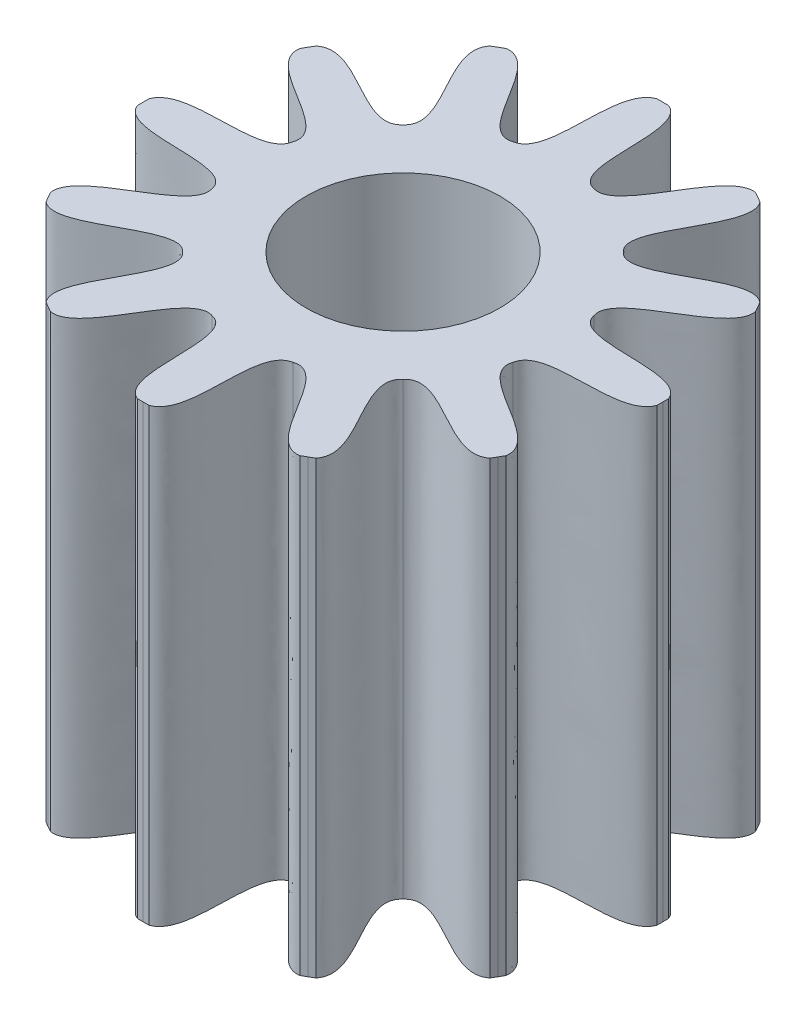
SolidWorks part; units mm, degrees
ref_plane "Alzado" through (0, 0, 0) normal (0, 0, 1) x (1, 0, 0)
ref_plane "Planta" through (0, 0, 0) normal (0, 1, 0) x (1, 0, 0)
ref_plane "Vista lateral" through (0, 0, 0) normal (1, 0, 0) x (0, 0, -1)
sketch "Sketch1" plane through (0, 0, 0) normal (0, 1, 0) x (1, 0, 0)
  line L0 (0, -1000) -> (0, 49000) construction
  line L1 (0, 0) -> (12940.9523, 48296.2913) construction
  line L2 (0, 0.75) -> (0.017, 0.7498)
  line L3 (0, 0.75) -> (-0.017, 0.7498)
  line L4 (0.375, 0.6495) -> (0.3602, 0.6579)
  line L5 (0.375, 0.6495) -> (0.3896, 0.6409)
  line L6 (0.6495, 0.375) -> (0.6409, 0.3896)
  line L7 (0.6495, 0.375) -> (0.6579, 0.3602)
  line L8 (0.75, 0) -> (0.7498, 0.017)
  line L9 (0.75, 0) -> (0.7498, -0.017)
  line L10 (0.6495, -0.375) -> (0.6579, -0.3602)
  line L11 (0.6495, -0.375) -> (0.6409, -0.3896)
  line L12 (0.375, -0.6495) -> (0.3896, -0.6409)
  line L13 (0.375, -0.6495) -> (0.3602, -0.6579)
  line L14 (0, -0.75) -> (0.017, -0.7498)
  line L15 (0, -0.75) -> (-0.017, -0.7498)
  line L16 (-0.375, -0.6495) -> (-0.3602, -0.6579)
  line L17 (-0.375, -0.6495) -> (-0.3896, -0.6409)
  line L18 (-0.6495, -0.375) -> (-0.6409, -0.3896)
  line L19 (-0.6495, -0.375) -> (-0.6579, -0.3602)
  line L20 (-0.75, 0) -> (-0.7498, -0.017)
  line L21 (-0.75, 0) -> (-0.7498, 0.017)
  line L22 (-0.6495, 0.375) -> (-0.6579, 0.3602)
  line L23 (-0.6495, 0.375) -> (-0.6409, 0.3896)
  line L24 (-0.375, 0.6495) -> (-0.3896, 0.6409)
  line L25 (-0.375, 0.6495) -> (-0.3602, 0.6579)
  circle A0 centre (0, 0) radius 0.75 construction
  circle A1 centre (0, 0) radius 0.45 construction
  spline S0 degree 3 poles (0.017, 0.7498) (0.1074, 0.7157) (0.0247, 0.4521) (0.1165, 0.4347) knots 0 0 0 0 1 1 1 1
  spline S1 degree 3 poles (-0.017, 0.7498) (-0.1074, 0.7157) (-0.0247, 0.4521) (-0.1165, 0.4347) knots 0 0 0 0 1 1 1 1
  spline S2 degree 3 poles (0.3602, 0.6579) (0.2649, 0.6735) (0.2047, 0.4039) (0.1165, 0.4347) knots 0 0 0 0 1 1 1 1
  spline S3 degree 3 poles (0.3896, 0.6409) (0.4509, 0.5661) (0.2474, 0.3792) (0.3182, 0.3182) knots 0 0 0 0 1 1 1 1
  spline S4 degree 3 poles (0.6409, 0.3896) (0.5661, 0.4509) (0.3792, 0.2474) (0.3182, 0.3182) knots 0 0 0 0 1 1 1 1
  spline S5 degree 3 poles (0.6579, 0.3602) (0.6735, 0.2649) (0.4039, 0.2047) (0.4347, 0.1165) knots 0 0 0 0 1 1 1 1
  spline S6 degree 3 poles (0.7498, 0.017) (0.7157, 0.1074) (0.4521, 0.0247) (0.4347, 0.1165) knots 0 0 0 0 1 1 1 1
  spline S7 degree 3 poles (0.7498, -0.017) (0.7157, -0.1074) (0.4521, -0.0247) (0.4347, -0.1165) knots 0 0 0 0 1 1 1 1
  spline S8 degree 3 poles (0.6579, -0.3602) (0.6735, -0.2649) (0.4039, -0.2047) (0.4347, -0.1165) knots 0 0 0 0 1 1 1 1
  spline S9 degree 3 poles (0.6409, -0.3896) (0.5661, -0.4509) (0.3792, -0.2474) (0.3182, -0.3182) knots 0 0 0 0 1 1 1 1
  spline S10 degree 3 poles (0.3896, -0.6409) (0.4509, -0.5661) (0.2474, -0.3792) (0.3182, -0.3182) knots 0 0 0 0 1 1 1 1
  spline S11 degree 3 poles (0.3602, -0.6579) (0.2649, -0.6735) (0.2047, -0.4039) (0.1165, -0.4347) knots 0 0 0 0 1 1 1 1
  spline S12 degree 3 poles (0.017, -0.7498) (0.1074, -0.7157) (0.0247, -0.4521) (0.1165, -0.4347) knots 0 0 0 0 1 1 1 1
  spline S13 degree 3 poles (-0.017, -0.7498) (-0.1074, -0.7157) (-0.0247, -0.4521) (-0.1165, -0.4347) knots 0 0 0 0 1 1 1 1
  spline S14 degree 3 poles (-0.3602, -0.6579) (-0.2649, -0.6735) (-0.2047, -0.4039) (-0.1165, -0.4347) knots 0 0 0 0 1 1 1 1
  spline S15 degree 3 poles (-0.3896, -0.6409) (-0.4509, -0.5661) (-0.2474, -0.3792) (-0.3182, -0.3182) knots 0 0 0 0 1 1 1 1
  spline S16 degree 3 poles (-0.6409, -0.3896) (-0.5661, -0.4509) (-0.3792, -0.2474) (-0.3182, -0.3182) knots 0 0 0 0 1 1 1 1
  spline S17 degree 3 poles (-0.6579, -0.3602) (-0.6735, -0.2649) (-0.4039, -0.2047) (-0.4347, -0.1165) knots 0 0 0 0 1 1 1 1
  spline S18 degree 3 poles (-0.7498, -0.017) (-0.7157, -0.1074) (-0.4521, -0.0247) (-0.4347, -0.1165) knots 0 0 0 0 1 1 1 1
  spline S19 degree 3 poles (-0.7498, 0.017) (-0.7157, 0.1074) (-0.4521, 0.0247) (-0.4347, 0.1165) knots 0 0 0 0 1 1 1 1
  spline S20 degree 3 poles (-0.6579, 0.3602) (-0.6735, 0.2649) (-0.4039, 0.2047) (-0.4347, 0.1165) knots 0 0 0 0 1 1 1 1
  spline S21 degree 3 poles (-0.6409, 0.3896) (-0.5661, 0.4509) (-0.3792, 0.2474) (-0.3182, 0.3182) knots 0 0 0 0 1 1 1 1
  spline S22 degree 3 poles (-0.3896, 0.6409) (-0.4509, 0.5661) (-0.2474, 0.3792) (-0.3182, 0.3182) knots 0 0 0 0 1 1 1 1
  spline S23 degree 3 poles (-0.3602, 0.6579) (-0.2649, 0.6735) (-0.2047, 0.4039) (-0.1165, 0.4347) knots 0 0 0 0 1 1 1 1
  point P4 (0, 0.75)
  point P8 (0.017, 0.7498)
  point P10 (0.1165, 0.4347)
  point P74 (0, 0)
  dimension "D1" = 1.5
  dimension "D2" = 0.3
  dimension "D3" = 15
  dimension "D4" = 0.017
  dimension "D5" = 12
extrude "Boss-Extrude1 (12 teeth)" add sketch "Sketch1" along normal blind 1.3
sketch "Sketch2" plane through (0, 0, 0) normal (0, 1, 0) x (1, 0, 0)
  circle A0 centre (0, 0) radius 0.28
  dimension "D1" = 0.56
extrude "Cut-Extrude1" cut sketch "Sketch2" along normal up to next
